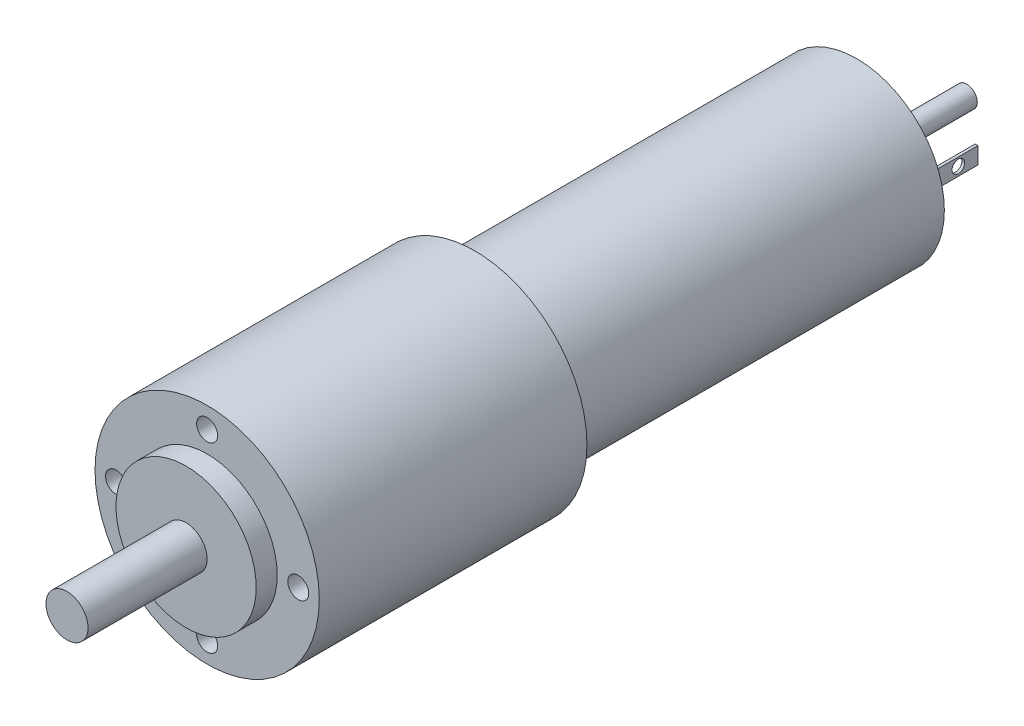
SolidWorks part; units mm, degrees
ref_plane "Plan de face" through (0, 0, 0) normal (0, 0, 1) x (1, 0, 0)
ref_plane "Plan de dessus" through (0, 0, 0) normal (0, 1, 0) x (1, 0, 0)
ref_plane "Plan de droite" through (0, 0, 0) normal (1, 0, 0) x (0, 0, -1)
sketch "Esquisse1" plane through (0, 0, 0) normal (0, 0, 1) x (1, 0, 0)
  circle A0 centre (0, 0) radius 16
extrude "Boss.-Extru.1" add sketch "Esquisse1" along normal blind 38.2
sketch "Esquisse4" plane through (0, 0, 0) normal (0, 0, -1) x (-1, 0, 0)
  circle A0 centre (0, 0) radius 12.5
extrude "Boss.-Extru.2" add sketch "Esquisse4" along normal blind 54.5
sketch "Esquisse5" plane through (0, 0, 38.2) normal (0, 0, 1) x (1, 0, 0)
  circle A0 centre (0, 0) radius 10
extrude "Boss.-Extru.3" add sketch "Esquisse5" along normal blind 3
sketch "Esquisse6" plane through (0, 0, 41.2) normal (0, 0, 1) x (1, 0, 0)
  circle A0 centre (0, 0) radius 3
extrude "Boss.-Extru.4" add sketch "Esquisse6" along normal blind 17
sketch "Esquisse8" plane through (0, 0, -54.5) normal (0, 0, -1) x (-1, 0, 0)
  circle A0 centre (0, 0) radius 4
extrude "Boss.-Extru.5" add sketch "Esquisse8" along normal blind 1.2
sketch "Esquisse9" plane through (0, 0, -55.7) normal (0, 0, -1) x (-1, 0, 0)
  circle A0 centre (0, 0) radius 3
extrude "Boss.-Extru.6" add sketch "Esquisse9" along normal blind 1.5
sketch "Esquisse10" plane through (0, 0, -57.2) normal (0, 0, -1) x (-1, 0, 0)
  circle A0 centre (0, 0) radius 1.5
extrude "Boss.-Extru.7" add sketch "Esquisse10" along normal blind 13
sketch "Esquisse11" plane through (0, 0, -54.5) normal (0, 0, -1) x (-1, 0, 0)
  line L0 (-25.65, 0.9) -> (21.4413, 0.9) construction
  line L1 (20.8423, 0) -> (-26.249, 0) construction
  line L2 (-25.65, -0.9) -> (21.4413, -0.9) construction
  line L4 (-8.6, 2.1) -> (-9, 2.1)
  line L5 (-8.6, 2.1) -> (-8.6, -0.3)
  line L6 (-8.6, -0.3) -> (-9, -0.3)
  line L7 (-9, 2.1) -> (-9, -0.3)
  line L8 (-8.6, 2.1) -> (-9, -0.3) construction
  line L9 (-8.6, -0.3) -> (-9, 2.1) construction
  point P7 (-8.8, 0.9)
  point P12 (0, 0)
  dimension "D1" = 0.9
  dimension "D2" = 0.4
  dimension "D3" = 8.8
  dimension "D4" = 2.4
extrude "Boss.-Extru.8" add sketch "Esquisse11" along normal blind 8.3
sketch "Esquisse14" plane through (9, 0, 0) normal (1, 0, 0) x (0, 0, -1)
  circle A0 centre (59.9979, 0.9262) radius 0.9
  dimension "D1" = 1.8
extrude "Enlèv. mat.-Extru.2" cut sketch "Esquisse14" against normal blind 1
pattern_circular "Répétition circulaire3" count 2 every 180 about axis through (0, 0, 0) along (0, 0, 1) of "Boss.-Extru.8"
pattern_circular "Répétition circulaire4" count 2 every 180 about axis through (0, 0, -59.9979) along (1, 0, 0) of "Enlèv. mat.-Extru.2"
sketch "Esquisse15" plane through (0, 0, -54.5) normal (0, 0, -1) x (-1, 0, 0)
  line L0 (0, 0) -> (-9.2621, 16.7092) construction
  line L2 (-19.3023, 0) -> (19.5894, 0) construction
  circle A0 centre (-4.2108, 7.5966) radius 0.8
  dimension "D1" = 61
extrude "Enlèv. mat.-Extru.3" cut sketch "Esquisse15" against normal blind 3
pattern_circular "Répétition circulaire5" count 2 every 180 about axis through (0, 0, 0) along (0, 0, 1) of "Enlèv. mat.-Extru.3"
sketch "Esquisse16" plane through (0, 0, 38.2) normal (0, 0, 1) x (1, 0, 0)
  line L0 (0, 0) -> (-29.8617, 0) construction
  circle A0 centre (-13, 0) radius 1.5
  dimension "D1" = 13
extrude "Enlèv. mat.-Extru.4" cut sketch "Esquisse16" against normal blind 4
pattern_circular "Répétition circulaire6" count 4 every 90 about axis through (0, 0, 0) along (0, 0, 1) of "Enlèv. mat.-Extru.4"
